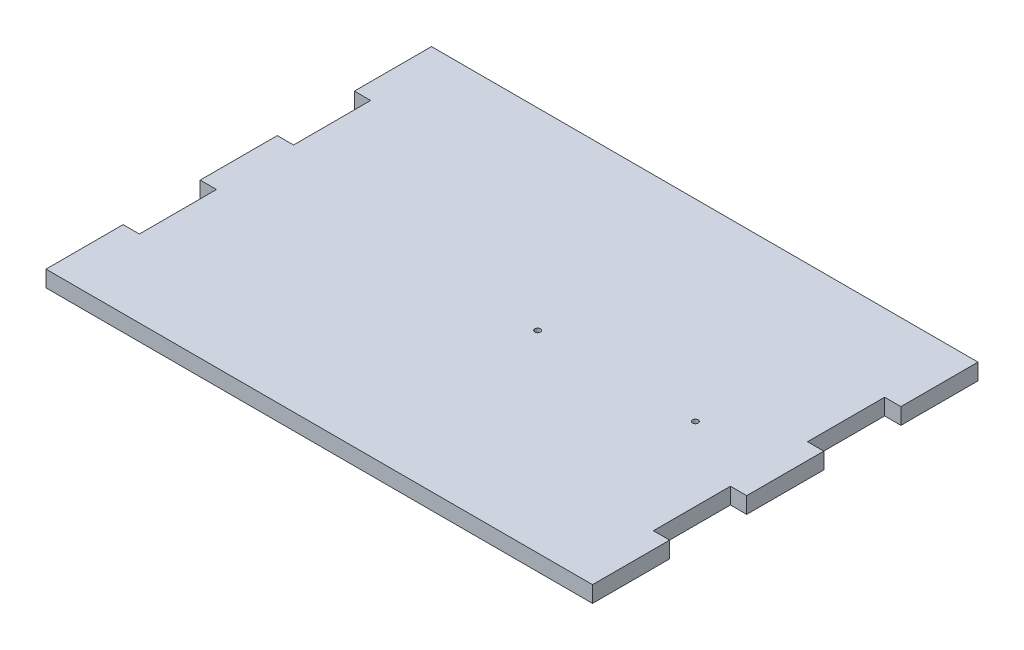
SolidWorks part; units mm, degrees
ref_plane "Front Plane" through (0, 0, 0) normal (0, 0, 1) x (1, 0, 0)
ref_plane "Top Plane" through (0, 0, 0) normal (0, 1, 0) x (1, 0, 0)
ref_plane "Right Plane" through (0, 0, 0) normal (1, 0, 0) x (0, 0, -1)
sketch "Sketch1" plane through (0, 0, 0) normal (0, 1, 0) x (1, 0, 0)
  line L0 (0, 0) -> (180, 0)
  line L1 (0, 100) -> (180, 100)
  line L2 (0, 0) -> (0, 100)
  line L4 (180, 0) -> (180, 100)
sketch "Sketch2" plane through (0, 0, 0) normal (0, 1, 0) x (1, 0, 0)
  line L1 (0, -6) -> (180, -6)
  line L2 (0, -6) -> (0, 106)
  line L3 (0, 106) -> (180, 106)
  line L4 (180, -6) -> (180, 106)
sketch "Sketch3" plane through (0, 0, 0) normal (0, 1, 0) x (1, 0, 0)
  line L1 (-6, -14) -> (186, -14)
  line L2 (-6, -14) -> (-6, 121)
  line L3 (-6, 121) -> (186, 121)
  line L4 (186, -14) -> (186, 121)
sketch "Sketch4" plane through (0, 0, 0) normal (0, 1, 0) x (1, 0, 0)
  line L0 (-5.7, 121.0017) -> (-5.7, 94)
  line L2 (-5.7, 94) -> (0, 94)
  line L3 (0, 0) -> (0, 100) construction
  line L4 (0, 94) -> (0, 67)
  line L5 (0, 67) -> (-5.7, 67)
  line L6 (-5.7, 67) -> (-5.7, 40)
  line L7 (-5.7, 40) -> (0, 40)
  line L8 (0, 40) -> (0, 13)
  line L9 (0, 13) -> (-5.7, 13)
  line L10 (-5.7, 13) -> (-5.7, -17)
  line L11 (-5.7, -17) -> (-9.7, -17)
  line L12 (-9.7, -17) -> (-9.7, 121.0017)
  line L13 (-9.7, 121.0017) -> (-5.7, 121.0017)
  line L14 (90, 131) -> (90, -20) construction
  line L15 (189.7, 121.0017) -> (185.7, 121.0017)
  line L16 (189.7, -17) -> (189.7, 121.0017)
  line L17 (185.7, -17) -> (189.7, -17)
  line L18 (185.7, 13) -> (185.7, -17)
  line L19 (180, 13) -> (185.7, 13)
  line L20 (180, 40) -> (180, 13)
  line L21 (185.7, 40) -> (180, 40)
  line L22 (185.7, 67) -> (185.7, 40)
  line L23 (180, 67) -> (185.7, 67)
  line L24 (180, 94) -> (180, 67)
  line L25 (185.7, 94) -> (180, 94)
  line L26 (185.7, 121.0017) -> (185.7, 94)
extrude "Boss-Extrude1" add sketch "Sketch3" along normal blind 5.7
extrude "Cut-Extrude1" cut sketch "Sketch4" along normal blind 6
ref_plane "Plane1" through (0, 5.7, 0) normal (0, 1, 0) x (1, 0, 0)
sketch "Sketch5" plane through (0, 5.7, 0) normal (0, 1, 0) x (1, 0, 0)
  line L0 (0, 0) -> (180, 0)
  line L1 (0, 100) -> (180, 100)
  line L2 (0, 0) -> (0, 100)
  line L4 (180, 0) -> (180, 100)
sketch "Sketch7" plane through (0, 5.7, 0) normal (0, 1, 0) x (1, 0, 0)
  line L1 (0, -6) -> (180, -6)
  line L2 (0, -6) -> (0, 106)
  line L3 (0, 106) -> (180, 106)
  line L4 (180, -6) -> (180, 106)
sketch "Sketch9" plane through (0, 0, 0) normal (0, 1, 0) x (1, 0, 0)
sketch "Sketch11" plane through (0, 0, 0) normal (0, 1, 0) x (1, 0, 0)
  line L1 (99, 53.5) -> (154.2, 53.5) construction
  circle A0 centre (99, 53.5) radius 1
  circle A1 centre (154.2, 53.5) radius 1
  point P0 (-6, 53.5)
extrude "Cut-Extrude2" cut sketch "Sketch11" along normal blind 33
